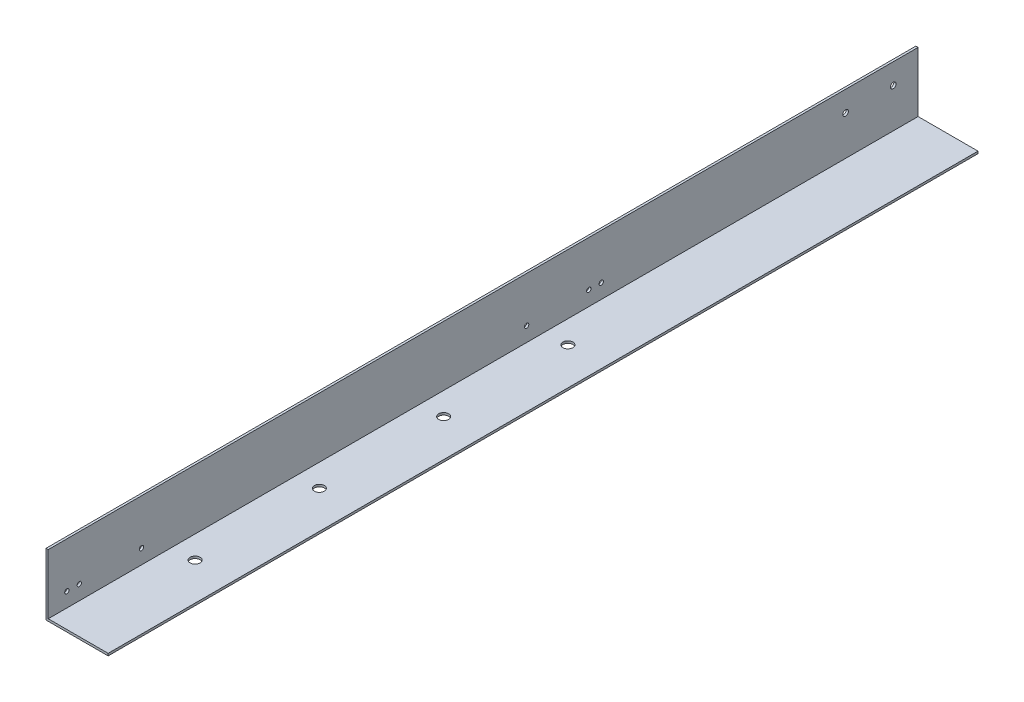
SolidWorks part; units mm, degrees
ref_plane "前基準面" through (0, 0, 0) normal (0, 0, 1) x (1, 0, 0)
ref_plane "上基準面" through (0, 0, 0) normal (0, 1, 0) x (1, 0, 0)
ref_plane "右基準面" through (0, 0, 0) normal (1, 0, 0) x (0, 0, -1)
sketch "草圖1" plane through (0, 0, 0) normal (0, 0, 1) x (1, 0, 0)
  line L0 (0, 50) -> (0, 0)
  line L1 (0, 0) -> (50, 0)
  line L2 (0, 50) -> (1.8, 50)
  line L3 (1.8, 50) -> (1.8, 1.8)
  line L4 (1.8, 1.8) -> (50, 1.8)
  line L5 (50, 1.8) -> (50, 0)
  dimension "D1" = 50
  dimension "D2" = 50
  dimension "D3" = 1.8
  dimension "D4" = 1.8
  dimension "D5" = 48.2
  dimension "D6" = 48.2
extrude "填料-伸長1" add sketch "草圖1" along normal blind 700 contours L0 L1 L5 L4 L3 L2
ref_plane "平面1" through (0, 0, 0) normal (0, -1, 0) x (-1, 0, 0)
ref_plane "平面2" through (0, 0, 0) normal (0, -1, 0) x (-1, 0, 0)
sketch "草圖2" plane through (0, 0, 0) normal (0, -1, 0) x (-1, 0, 0)
  line L6 (-20, -700) -> (-20, -300) construction
  line L7 (0, -700) -> (-50, -700) construction
  line L8 (0, -700) -> (0, 0) construction
  circle A0 centre (-20, -300) radius 4
  circle A1 centre (-20, -600) radius 4
  circle A2 centre (-20, -500) radius 4
  circle A3 centre (-20, -400) radius 4
  dimension "D1" = 20
  dimension "D2" = 8
  dimension "D3" = 100
  dimension "D4" = 8
  dimension "D5" = 400
  dimension "D8" = 8
  dimension "D9" = 8
  dimension "D6" = 200
  dimension "D7" = 300
extrude "除料-伸長1" cut sketch "草圖2" against normal blind 10
sketch "草圖3" plane through (0, 0, 0) normal (-1, 0, 0) x (0, 0, 1)
  line L0 (700, 33.5) -> (0, 33.5) construction
  line L1 (700, 50) -> (700, 0) construction
  line L3 (0, 50) -> (0, 0) construction
  line L4 (700, 50) -> (0, 50) construction
  circle A2 centre (58.34, 33.5) radius 2.25
  circle A3 centre (20, 33.5) radius 2.25
  dimension "D2" = 20
  dimension "D4" = 4.5
  dimension "D5" = 4.5
  dimension "D1" = 16.5
  dimension "D3" = 38.34
extrude "除料-伸長2" cut sketch "草圖3" against normal through all
hole_wizard "Ø3.5 (3.5) 直徑孔1" positions "草圖6" profile "草圖5" hole size "Ø3.5" standard "JIS"
sketch "草圖6" plane through (0, 0, 0) normal (-1, 0, 0) x (0, 0, 1)
  line L0 (700, 13.5) -> (0, 13.5) construction
  line L1 (700, 50) -> (700, 0) construction
  line L2 (0, 50) -> (0, 0) construction
  line L5 (700, 0) -> (0, 0) construction
  point P17 (685, 13.5)
  point P19 (675, 13.5)
  point P21 (625, 13.5)
  point P30 (255, 13.5)
  point P33 (265, 13.5)
  point P35 (315, 13.5)
  dimension "D1" = 13.5
  dimension "D2" = 15
  dimension "D3" = 10
  dimension "D4" = 50
  dimension "D5" = 445
  dimension "D6" = 50
  dimension "D7" = 10
sketch "草圖5" plane through (0, 13.5, 685) normal (0, 1, 0) x (0, 0, 1)
  line L0 (0, 0) -> (0, 3.0515)
  line L1 (0, 3.0515) -> (1.75, 2)
  line L2 (1.75, 2) -> (1.75, 0)
  line L5 (1.75, 0) -> (0, 0)
  line L10 (0, 3.0515) -> (-1.75, 2) construction
  line L11 (0, -6.35) -> (0, 107.95) construction
  dimension "鑽孔直徑" = 3.5
  dimension "鑽孔深度" = 2
  dimension "導頭角度" = 118
